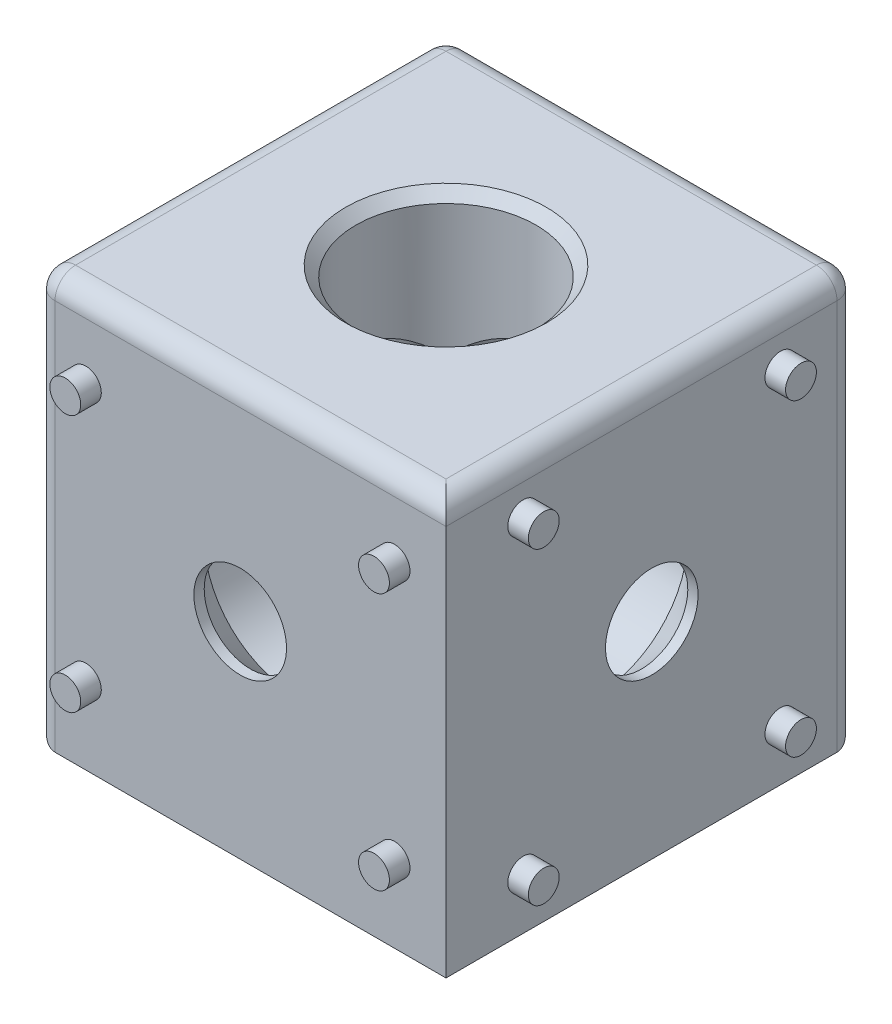
SolidWorks part; units mm, degrees
material "Алюминиевый сплав"
ref_plane "Спереди" through (0, 0, 0) normal (0, 0, 1) x (1, 0, 0)
ref_plane "Сверху" through (0, 0, 0) normal (0, 1, 0) x (1, 0, 0)
ref_plane "Справа" through (0, 0, 0) normal (1, 0, 0) x (0, 0, -1)
sketch "Эскиз1" plane through (0, 0, 0) normal (0, 1, 0) x (1, 0, 0)
  line L1 (-20, -20) -> (20, -20)
  line L2 (-20, -20) -> (-20, 20)
  line L3 (-20, 20) -> (20, 20)
  line L4 (20, -20) -> (20, 20)
  line L5 (-20, -20) -> (20, 20) construction
  line L6 (-20, 20) -> (20, -20) construction
  point P0 (0, 0)
  dimension "D1" = 40
extrude "Бобышка-Вытянуть1" add sketch "Эскиз1" along normal mid plane 40
sketch "Эскиз4" plane through (0, 0, 0) normal (0, 0, 1) x (1, 0, 0)
  line L0 (-4.5, -20) -> (-4.5, -19)
  line L1 (-20, -20) -> (20, -20) construction
  line L2 (-4.5, -19) -> (-8.75, -14.75)
  line L3 (-8.75, -14.75) -> (-8.75, 19)
  line L4 (-20, 20) -> (20, 20) construction
  line L6 (0, 20) -> (0, -20) construction
  line L7 (0, -20) -> (-4.5, -20)
  line L8 (0, 20) -> (0, -20)
  line L9 (-8.75, 19) -> (-9.75, 20)
  line L10 (-9.75, 20) -> (0, 20)
  dimension "D1" = 9
  dimension "D2" = 45
  dimension "D3" = 17.5
  dimension "D4" = 1
  dimension "D5" = 1
revolve "Вырез-Повернуть1" cut sketch "Эскиз4" angle 360 about L6
sketch "Эскиз5" plane through (0, -20, 0) normal (0, -1, 0) x (1, 0, 0)
  line L1 (-15, 12.5) -> (15, 12.5) construction
  line L2 (-15, 12.5) -> (-15, -12.5) construction
  line L3 (-15, -12.5) -> (15, -12.5) construction
  line L4 (15, 12.5) -> (15, -12.5) construction
  circle A0 centre (-15, 12.5) radius 1.5
  circle A1 centre (-15, -12.5) radius 1.5
  circle A2 centre (15, -12.5) radius 1.5
  circle A3 centre (15, 12.5) radius 1.5
  point P5 (-15, 0)
  point P12 (0, 12.5)
  dimension "D1" = 3
  dimension "D2" = 30
  dimension "D3" = 25
extrude "Бобышка-Вытянуть2" add sketch "Эскиз5" along normal blind 2
ref_plane "Плоскость1" through (0, 0, 0) normal (0.7071, 0.7071, 0) x (0.7071, -0.7071, 0)
ref_plane "Плоскость2" through (0, 0, 0) normal (0, 0.7071, 0.7071) x (1, 0, 0)
mirror "Зеркальное отражение1" about plane through (0, 0, 0) normal (0.7071, 0.7071, 0) of "Бобышка-Вытянуть2", "Вырез-Повернуть1"
fillet "Скругление1" radius 2 9 edges at (-20, -20, 0) (20, 20, 0) (-20, 0, 20) (0, 20, 20) (-20, 20, 0) (-20, 0, -20) (0, 20, -20) (0, -20, -20) (20, 0, -20)
mirror "Зеркальное отражение2" about plane through (0, 0, 0) normal (0, 0.7071, 0.7071) of "Бобышка-Вытянуть2", "Вырез-Повернуть1"
